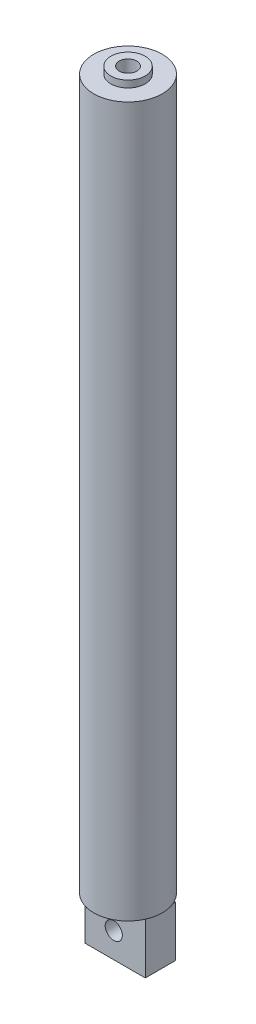
SolidWorks part; units mm, degrees
ref_plane "Alzado" through (0, 0, 0) normal (0, 0, 1) x (1, 0, 0)
ref_plane "Planta" through (0, 0, 0) normal (0, 1, 0) x (1, 0, 0)
ref_plane "Vista lateral" through (0, 0, 0) normal (1, 0, 0) x (0, 0, -1)
sketch "Croquis1" plane through (0, 0, 0) normal (0, 1, 0) x (1, 0, 0)
  circle A0 centre (0, 0) radius 6.35
  dimension "D1" = 12.7
extrude "Saliente-Extruir1" add sketch "Croquis1" along normal blind 127
sketch "Croquis2" plane through (0, 0, 0) normal (0, 1, 0) x (1, 0, 0)
  circle A0 centre (0, 0) radius 3.175
  dimension "D1" = 6.35
extrude "Saliente-Extruir2" add sketch "Croquis2" along normal blind 128.27
sketch "Croquis3" plane through (0, 0, 0) normal (0, 1, 0) x (1, 0, 0)
  circle A0 centre (0, 0) radius 1.6256
  dimension "D1" = 3.2512
extrude "Cortar-Extruir1" cut sketch "Croquis3" along normal blind 135.128 and the other way blind 0.254
sketch "Croquis4" plane through (0, 0, 0) normal (0, -1, 0) x (-1, 0, 0)
  circle A0 centre (0, 0) radius 6.35
extrude "Saliente-Extruir3" add sketch "Croquis4" along normal blind 4.318
sketch "Croquis5" plane through (0, 0, 0) normal (1, 0, 0) x (0, 0, -1)
  line L0 (-2.6426, -13.6956) -> (-2.6426, -4.318)
  line L1 (-6.35, -4.318) -> (6.35, -4.318) construction
  line L2 (2.9372, -4.318) -> (2.9372, -13.6956)
  line L3 (2.9372, -13.6956) -> (-2.6426, -13.6956)
  line L4 (-2.6426, -4.318) -> (2.9372, -4.318)
extrude "Saliente-Extruir5" add sketch "Croquis5" along normal blind 5.842 and the other way blind 5.334
sketch "Croquis8" plane through (0, 0, 0) normal (0, 0, 1) x (1, 0, 0)
  circle A0 centre (0, -9.0068) radius 1.5875
  dimension "D1" = 3.175
extrude "Cortar-Extruir2" cut sketch "Croquis8" along normal blind 23.876 and the other way blind 64.262
